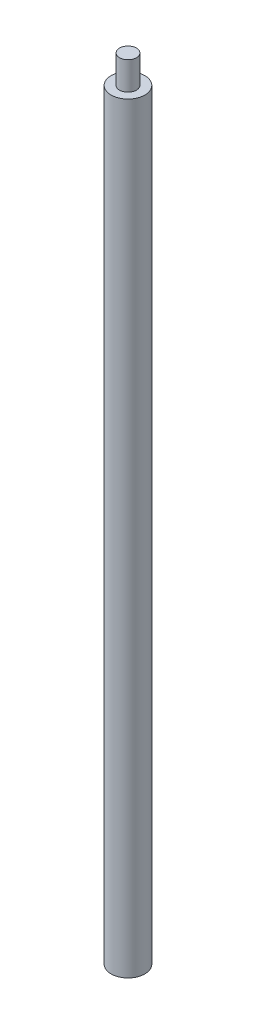
SolidWorks part; units mm, degrees
ref_plane "Plano frontal" through (0, 0, 0) normal (0, 0, 1) x (1, 0, 0)
ref_plane "Plano superior" through (0, 0, 0) normal (0, 1, 0) x (1, 0, 0)
ref_plane "Plano direito" through (0, 0, 0) normal (1, 0, 0) x (0, 0, -1)
sketch "Esboço1" plane through (0, 0, 0) normal (0, 1, 0) x (1, 0, 0)
  circle A0 centre (0, 0) radius 3
  dimension "D1" = 6
extrude "Ressalto-extrusão1" add sketch "Esboço1" along normal blind 135.5
sketch "Esboço2" plane through (0, 0, 0) normal (0, -1, 0) x (1, 0, 0)
  point P0 (0, 0)
hole_wizard "Furo roscado de M3x0.51" positions "Esboço4" profile "Esboço3" tap size "M3x0.5" standard "Ansi Metric"
sketch "Esboço4" plane through (0, 0, 0) normal (0, -1, 0) x (1, 0, 0)
  point P0 (0, 0)
sketch "Esboço3" plane through (0, 0, 0) normal (1, 0, 0) x (0, 0, -1)
  line L0 (0, 0) -> (0, 19.2511)
  line L1 (0, 19.2511) -> (1.25, 18.5)
  line L2 (1.25, 18.5) -> (1.25, 0)
  line L5 (1.25, 0) -> (0, 0)
  line L10 (0, 19.2511) -> (-1.25, 18.5) construction
  line L11 (0, -6.35) -> (0, 107.95) construction
  dimension "Tap Drill Dia." = 2.5
  dimension "Tap Drill Depth" = 18.5
  dimension "Drill Angle" = 118
cosmetic thread "Rosca de furo1" parameters "D1"=6, "D2"=3
sketch "Esboço10" plane through (0, 135.5, 0) normal (0, 1, 0) x (1, 0, 0)
  circle A0 centre (0, 0) radius 1.5
  dimension "D1" = 3
extrude "Ressalto-extrusão2" add sketch "Esboço10" along normal blind 5
